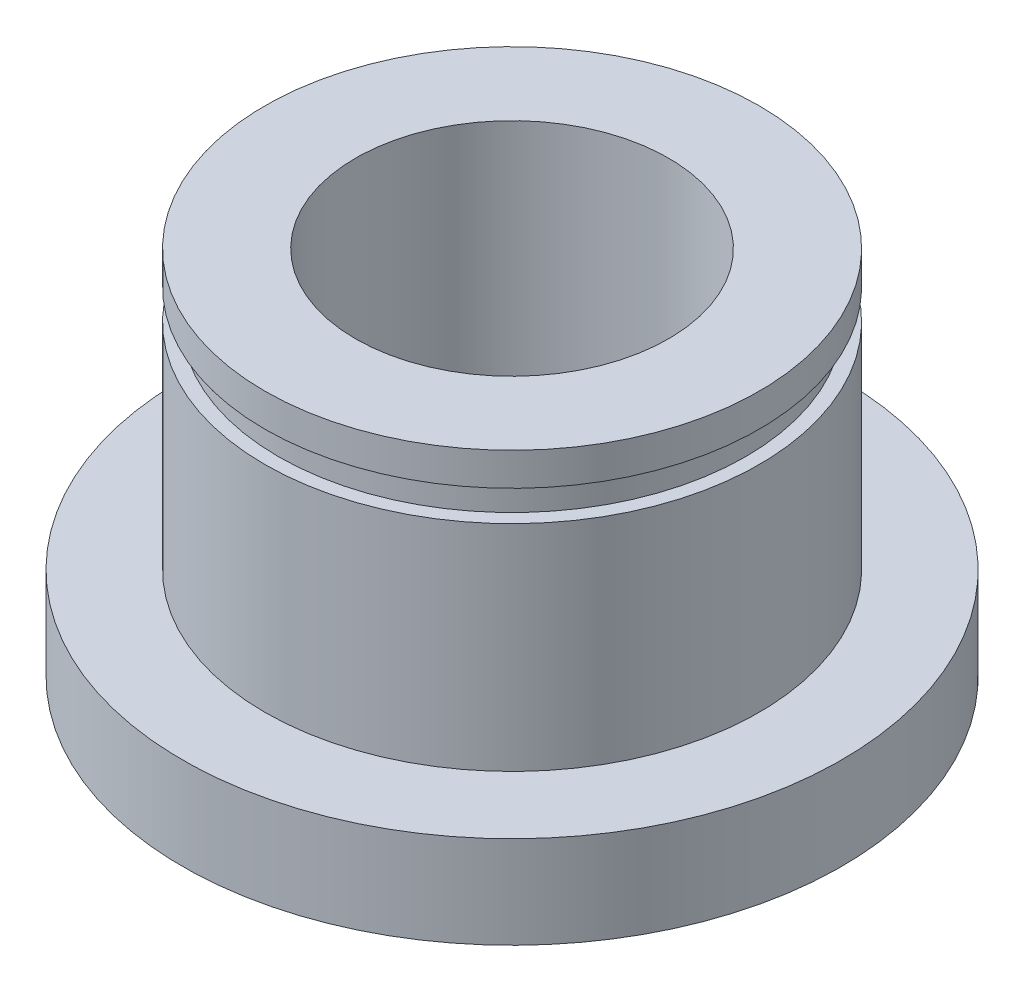
SolidWorks part; units mm, degrees
material "7075-T6 (SN)"
ref_plane "X-Y Datum" through (0, 0, 0) normal (0, 0, 1) x (1, 0, 0)
ref_plane "X-Z Datum" through (0, 0, 0) normal (0, 1, 0) x (1, 0, 0)
ref_plane "Y-Z Datum" through (0, 0, 0) normal (1, 0, 0) x (0, 0, -1)
sketch "Sketch1" plane through (0, 0, 0) normal (1, 0, 0) x (0, 0, -1)
  line L0 (0, 0) -> (0, 8253.6099) construction
  line L1 (0, -4.4609) -> (-7.9375, -4.4609)
  line L2 (-7.9375, -4.4609) -> (-7.9375, -2.2384)
  line L3 (-7.9375, -2.2384) -> (-5.9531, -2.2384)
  line L4 (-5.9531, -2.2384) -> (-5.9531, 2.9305)
  line L7 (-5.6261, 3.6671) -> (-5.9531, 3.6671)
  line L8 (-5.9531, 3.6671) -> (-5.9531, 4.4609)
  line L9 (-5.9531, 4.4609) -> (0, 4.4609)
  line L10 (0, 4.4609) -> (0, -4.4609)
  line L11 (0, 0) -> (-50000, 0) construction
  line L12 (-5.9531, 2.9305) -> (-5.6261, 2.9305)
  line L13 (-5.6261, 2.9305) -> (-5.6261, 3.6671)
  point P9 (0, 0)
  dimension "D1" = 15.875
  dimension "D2" = 11.9062
  dimension "D3" = 2.2225
  dimension "D4" = 11.2522
  dimension "D5" = 0.7937
  dimension "D6" = 5.1689
  dimension "D7" = 0.7366
revolve "Revolve1" add sketch "Sketch1" angle 360 about L0
hole_wizard "19/64 (0.29688) Diameter Hole1" positions "Sketch2" profile "Sketch3" hole size "19/64" standard "ANSI Inch" end condition through all
sketch "Sketch2" plane through (0, 4.4609, 0) normal (0, 1, 0) x (1, 0, 0)
  point P0 (0, 0)
sketch "Sketch3" plane through (0, 4.4609, 0) normal (1, 0, 0) x (0, 0, 1)
  line L0 (0, 0) -> (0, 8.9218)
  line L1 (0, 8.9218) -> (3.7704, 8.9218)
  line L2 (3.7704, 8.9218) -> (3.7704, 0)
  line L5 (3.7704, 0) -> (0, 0)
  line L11 (0, -6.35) -> (0, 107.95) construction
  dimension "Thru Hole Dia." = 7.5408
  dimension "Thru Hole Depth" = 8.9218
chamfer "Chamfer1" distance 0.7937 angle 45 1 edges at (0, -4.4609, 3.7704)
